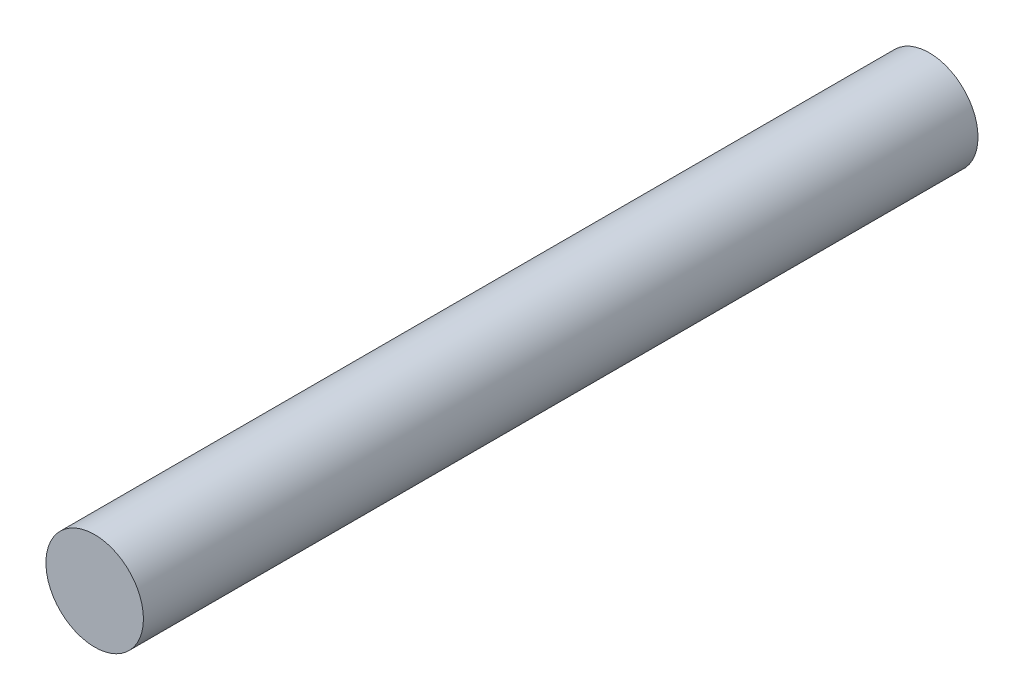
SolidWorks part; units mm, degrees
ref_plane "Front Plane" through (0, 0, 0) normal (0, 0, 1) x (1, 0, 0)
ref_plane "Top Plane" through (0, 0, 0) normal (0, 1, 0) x (1, 0, 0)
ref_plane "Right Plane" through (0, 0, 0) normal (1, 0, 0) x (0, 0, -1)
sketch "Sketch1" plane through (0, 0, 0) normal (0, 0, 1) x (1, 0, 0)
  circle A0 centre (0, 0) radius 2.775
  dimension "D1" = 5.55
extrude "Boss-Extrude1" add sketch "Sketch1" along normal blind 47.5
